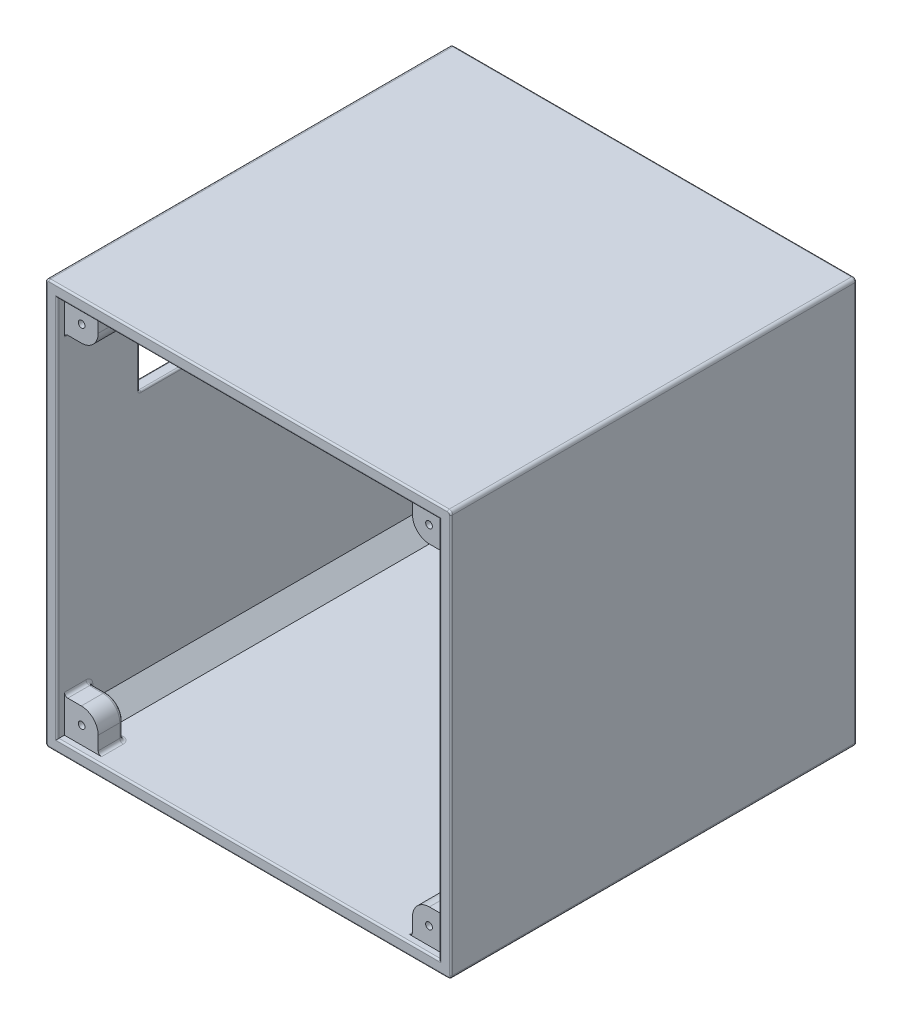
SolidWorks part; units mm, degrees
material "PVC 0.007 Plasticizado"
ref_plane "MESA" through (0, 0, 0) normal (0, 0, 1) x (1, 0, 0)
ref_plane "Plano superior" through (0, 0, 0) normal (0, 1, 0) x (1, 0, 0)
ref_plane "Plano direito" through (0, 0, 0) normal (1, 0, 0) x (0, 0, -1)
sketch "Esboço2" plane through (0, 0, 0) normal (0, 0, 1) x (1, 0, 0)
  line L1 (-60, -60) -> (60, -60)
  line L2 (-60, -60) -> (-60, 60)
  line L3 (-60, 60) -> (60, 60)
  line L4 (60, -60) -> (60, 60)
  line L5 (-60, -60) -> (60, 60) construction
  line L6 (-60, 60) -> (60, -60) construction
  point P0 (0, 0)
extrude "Ressalto-extrusão1" add sketch "Esboço2" along normal blind 120
sketch "Esboço3" plane through (0, 0, 120) normal (0, 0, 1) x (1, 0, 0)
  line L8 (56.5, -56.5) -> (56.5, 56.5)
  line L9 (56.5, 56.5) -> (-56.5, 56.5)
  line L10 (-56.5, 56.5) -> (-56.5, -56.5)
  line L11 (-56.5, -56.5) -> (56.5, -56.5)
  line L12 (56.5, -56.5) -> (56.5, 56.5)
  line L13 (56.5, 56.5) -> (-56.5, 56.5)
  line L14 (-56.5, 56.5) -> (-56.5, -56.5)
  line L15 (-56.5, -56.5) -> (56.5, -56.5)
  dimension "D1" = 3.5
extrude "Corte-extrusão1" cut sketch "Esboço3" against normal blind 120
ref_plane "Plano1" through (0, 0, 0) normal (0, 0, 1) x (1, 0, 0)
ref_plane "Plano2" through (0, 0, 116.5) normal (0, 0, 1) x (1, 0, 0)
sketch "Esboço4" plane through (0, 0, 0) normal (0, 0, 1) x (1, 0, 0)
  line L0 (56.5, 56.5) -> (-56.5, 56.5) construction
  line L1 (-56.5, 56.5) -> (-56.5, -56.5) construction
  line L2 (-51.5, 46.5) -> (-56.5, 46.5)
  line L3 (-56.5, 46.5) -> (-56.5, 56.5)
  line L4 (-56.5, 56.5) -> (-46.5, 56.5)
  line L5 (-46.5, 56.5) -> (-46.5, 51.5)
  line L6 (0, -55) -> (0, 55) construction
  line L7 (46.5, 56.5) -> (46.5, 51.5)
  line L8 (56.5, 56.5) -> (46.5, 56.5)
  line L9 (56.5, 46.5) -> (56.5, 56.5)
  line L10 (51.5, 46.5) -> (56.5, 46.5)
  line L11 (55, 0) -> (-55, 0) construction
  line L12 (51.5, -46.5) -> (56.5, -46.5)
  line L13 (56.5, -46.5) -> (56.5, -56.5)
  line L14 (56.5, -56.5) -> (46.5, -56.5)
  line L15 (46.5, -56.5) -> (46.5, -51.5)
  line L16 (-46.5, -56.5) -> (-46.5, -51.5)
  line L17 (-56.5, -56.5) -> (-46.5, -56.5)
  line L18 (-56.5, -46.5) -> (-56.5, -56.5)
  line L19 (-51.5, -46.5) -> (-56.5, -46.5)
  line L20 (-51.5, 5) -> (-56.5, 5)
  line L21 (-56.5, 5) -> (-56.5, -5)
  line L22 (-56.5, -5) -> (-51.5, -5)
  line L23 (56.5, -5) -> (51.5, -5)
  line L24 (56.5, 5) -> (56.5, -5)
  line L25 (51.5, 5) -> (56.5, 5)
  line L26 (-5, 51.5) -> (-5, 56.5)
  line L27 (-5, 56.5) -> (5, 56.5)
  line L28 (5, 56.5) -> (5, 51.5)
  arc A0 (-51.5, 46.5) -> (-46.5, 51.5) centre (-51.5, 51.5) ccw
  arc A1 (51.5, 46.5) -> (46.5, 51.5) centre (51.5, 51.5) cw
  arc A2 (51.5, -46.5) -> (46.5, -51.5) centre (51.5, -51.5) ccw
  arc A3 (-51.5, -46.5) -> (-46.5, -51.5) centre (-51.5, -51.5) cw
  arc A4 (-51.5, -5) -> (-51.5, 5) centre (-51.5, 0) ccw
  arc A5 (51.5, -5) -> (51.5, 5) centre (51.5, 0) cw
  arc A6 (-5, 51.5) -> (5, 51.5) centre (0, 51.5) ccw
  dimension "D1" = 10
  dimension "D2" = 10
  dimension "D3" = 10
extrude "Ressalto-extrusão2" add sketch "Esboço4" along normal blind 7
sketch "Esboço5" plane through (0, 0, 116.5) normal (0, 0, 1) x (1, 0, 0)
  line L0 (-51.5, 46.5) -> (-56.5, 46.5)
  line L1 (-56.5, 46.5) -> (-56.5, 56.5)
  line L2 (-56.5, 56.5) -> (-46.5, 56.5)
  line L3 (-46.5, 56.5) -> (-46.5, 51.5)
  line L4 (46.5, 56.5) -> (46.5, 51.5)
  line L5 (56.5, 56.5) -> (46.5, 56.5)
  line L6 (56.5, 46.5) -> (56.5, 56.5)
  line L7 (51.5, 46.5) -> (56.5, 46.5)
  line L8 (51.5, -46.5) -> (56.5, -46.5)
  line L9 (56.5, -46.5) -> (56.5, -56.5)
  line L10 (56.5, -56.5) -> (46.5, -56.5)
  line L11 (46.5, -56.5) -> (46.5, -51.5)
  line L12 (-46.5, -56.5) -> (-46.5, -51.5)
  line L13 (-56.5, -56.5) -> (-46.5, -56.5)
  line L14 (-56.5, -46.5) -> (-56.5, -56.5)
  line L15 (-51.5, -46.5) -> (-56.5, -46.5)
  arc A0 (-51.5, 46.5) -> (-46.5, 51.5) centre (-51.5, 51.5) ccw
  arc A1 (51.5, 46.5) -> (46.5, 51.5) centre (51.5, 51.5) cw
  arc A2 (51.5, -46.5) -> (46.5, -51.5) centre (51.5, -51.5) ccw
  arc A3 (-51.5, -46.5) -> (-46.5, -51.5) centre (-51.5, -51.5) cw
  dimension "D1" = 10
ref_plane "Plano5" through (0, 0, 117.9) normal (0, 0, 1) x (1, 0, 0)
sketch "Esboço13" plane through (0, 0, 0) normal (0, 0, 1) x (1, 0, 0)
  line L0 (-56.5, -56.5) -> (56.5, -56.5) construction
  line L1 (-5, -51.5) -> (-5, -56.5)
  line L2 (-5, -56.5) -> (5, -56.5)
  line L3 (5, -56.5) -> (5, -51.5)
  arc A0 (5, -51.5) -> (-5, -51.5) centre (0, -51.5) ccw
  dimension "D1" = 10
extrude "Ressalto-extrusão6" add sketch "Esboço13" along normal blind 7
chamfer "Chanfro1" distance 5 angle 45 1 edges at (-56.5, 56.5, 63.5)
chamfer "Chanfro2" distance 5 angle 45 3 edges at (-56.5, -56.5, 63.5) (56.5, -56.5, 63.5) (56.5, 56.5, 63.5)
sketch "Esboço14" plane through (-60, 0, 0) normal (-1, 0, 0) x (0, 0, 1)
  line L0 (120, 60) -> (0, 60) construction
  line L1 (24.25, 45) -> (95.75, 45)
  line L2 (24.25, 45) -> (24.25, 20.5)
  line L3 (24.25, 20.5) -> (95.75, 20.5)
  line L4 (95.75, 45) -> (95.75, 20.5)
  line L5 (24.25, 45) -> (95.75, 20.5) construction
  line L6 (24.25, 20.5) -> (95.75, 45) construction
  point P0 (60, 32.75)
  point P8 (60, 60)
  dimension "D1" = 71.5
  dimension "D2" = 24.5
  dimension "D3" = 15
extrude "Corte-extrusão6" cut sketch "Esboço14" against normal blind 10
sketch "Esboço15" plane through (0, 0, 120) normal (0, 0, 1) x (1, 0, 0)
  line L1 (-56.5, -56.5) -> (56.5, -56.5)
  line L2 (-56.5, -56.5) -> (-56.5, 56.5)
  line L3 (-56.5, 56.5) -> (56.5, 56.5)
  line L4 (56.5, -56.5) -> (56.5, 56.5)
  line L5 (-56.5, -56.5) -> (56.5, 56.5) construction
  line L6 (-56.5, 56.5) -> (56.5, -56.5) construction
  point P0 (0, 0)
  dimension "D1" = 113
extrude "Corte-extrusão7" cut sketch "Esboço15" against normal blind 5
fillet "Filete3" radius 1 1 edges at (-60, 60, 60)
fillet "Filete4" radius 1 3 edges at (60, 60, 60) (60, -60, 60) (-60, -60, 60)
extrude "Ressalto-extrusão7" add sketch "Esboço5" against normal blind 6 and the other way blind 1.4
fillet "Filete8" radius 1 88 edges at (56.5, 46.5, 3.5) (46.5, 56.5, 3.5) (54, 46.5, 7) (47.9645, 47.9645, 7) (46.5, 54, 7) (49, 56.5, 7) (54, 54, 7) (56.5, 49, 7) (56.5, -46.5, 114.2) (46.5, -56.5, 114.2) (-46.5, -56.5, 114.2) (-56.5, -46.5, 114.2) (-56.5, 46.5, 114.2) (-46.5, 56.5, 114.2) (46.5, 56.5, 114.2) (56.5, 46.5, 114.2) (56.5, 5, 3.5) (56.5, -5, 3.5) (46.5, -56.5, 3.5) (56.5, -46.5, 3.5) (5, -56.5, 3.5) (-5, -56.5, 3.5) (-56.5, -46.5, 3.5) (-46.5, -56.5, 3.5) (-56.5, -5, 3.5) (-56.5, 5, 3.5) (-46.5, 56.5, 3.5) (-56.5, 46.5, 3.5) (-5, 56.5, 3.5) (5, 56.5, 3.5) (54, -46.5, 110.5) (47.9645, -47.9645, 110.5) (46.5, -54, 110.5) (49, -56.5, 110.5) (54, -54, 110.5) (56.5, -49, 110.5) (-49, -56.5, 110.5) (-46.5, -54, 110.5) (-47.9645, -47.9645, 110.5) (-54, -46.5, 110.5) (-56.5, -49, 110.5) (-54, -54, 110.5) (-54, 46.5, 110.5) (-47.9645, 47.9645, 110.5) (-46.5, 54, 110.5) (-49, 56.5, 110.5) (-54, 54, 110.5) (-56.5, 49, 110.5) (49, 56.5, 110.5) (46.5, 54, 110.5) (47.9645, 47.9645, 110.5) (54, 46.5, 110.5) (56.5, 49, 110.5) (54, 54, 110.5) (54, 5, 7) (56.5, 0, 7) (54, -5, 7) (46.5, 0, 7) (46.5, -54, 7) (47.9645, -47.9645, 7) (54, -46.5, 7) (56.5, -49, 7) (54, -54, 7) (49, -56.5, 7) (5, -54, 7) (0, -56.5, 7) (-5, -54, 7) (0, -46.5, 7) (-54, -46.5, 7) (-47.9645, -47.9645, 7) (-46.5, -54, 7) (-49, -56.5, 7) (-54, -54, 7) (-56.5, -49, 7) (-54, -5, 7) (-56.5, 0, 7) (-54, 5, 7) (-46.5, 0, 7) (-46.5, 54, 7) (-47.9645, 47.9645, 7) (-54, 46.5, 7) (-56.5, 49, 7) (-54, 54, 7) (-49, 56.5, 7) (0, 46.5, 7) (-5, 54, 7) (0, 56.5, 7) (5, 54, 7)
sketch "Esboço16" plane through (0, 0, 117.9) normal (0, 0, 1) x (1, 0, 0)
  line L0 (59, 60) -> (-59, 60) construction
  line L1 (-60, 59) -> (-60, -59) construction
  circle A0 centre (-51.4, 51.4) radius 1
  dimension "D1" = 2
  dimension "D2" = 8.6
  dimension "D3" = 8.6
extrude "Corte-extrusão8" cut sketch "Esboço16" against normal up to next (7.4 mm away)
mirror "Espelhar1" about plane through (0, 0, 0) normal (0, 1, 0) of "Corte-extrusão8"
mirror "Espelhar2" about plane through (0, 0, 0) normal (1, 0, 0) of "Espelhar1", "Corte-extrusão8"
sketch "Esboço17" plane through (0, 0, 7) normal (0, 0, 1) x (1, 0, 0)
  line L0 (59, 60) -> (-59, 60) construction
  line L1 (-60, 59) -> (-60, -59) construction
  circle A0 centre (-51.4, 51.4) radius 1.75
  dimension "D1" = 8.6
  dimension "D2" = 8.6
extrude "Corte-extrusão9" cut sketch "Esboço17" against normal up to next (7 mm away)
sketch "Esboço18" plane through (0, 0, 7) normal (0, 0, 1) x (1, 0, 0)
  circle A0 centre (-51.4, 51.4) radius 3.6
  dimension "D1" = 7.2
extrude "Corte-extrusão10" cut sketch "Esboço18" against normal blind 1 and the other way blind 1
mirror "Espelhar5" about plane through (0, 0, 0) normal (0, 1, 0) of "Corte-extrusão10", "Corte-extrusão9"
mirror "Espelhar6" about plane through (0, 0, 0) normal (1, 0, 0) of "Espelhar5", "Corte-extrusão9", "Corte-extrusão10"
sketch "Esboço19" plane through (0, 0, 7) normal (0, 0, 1) x (1, 0, 0)
  line L0 (-60, 59) -> (-60, -59) construction
  line L2 (59, 60) -> (-59, 60) construction
  line L3 (60, -59) -> (60, 59) construction
  line L5 (-59, -60) -> (59, -60) construction
  circle A0 centre (-51.4, 0) radius 3.6
  circle A4 centre (0, 51.4) radius 3.6
  circle A5 centre (51.4, 0) radius 3.6
  circle A6 centre (0, -51.4) radius 3.6
  dimension "D1" = 8.6
  dimension "D3" = 8.6
  dimension "D4" = 7.2
  dimension "D5" = 7.2
  dimension "D6" = 7.2
  dimension "D7" = 7.2
  dimension "8.6" = 8.6
  dimension "D2" = 8.6
extrude "Corte-extrusão12" cut sketch "Esboço19" against normal blind 0.5
sketch "Esboço21" plane through (0, 0, 6.5) normal (0, 0, 1) x (1, 0, 0)
  line L1 (59, 60) -> (-59, 60) construction
  line L2 (60, -59) -> (60, 59) construction
  line L3 (-59, -60) -> (59, -60) construction
  circle A0 centre (-51.4, 0) radius 1.75
  circle A1 centre (0, 51.4) radius 1.75
  circle A2 centre (51.4, 0) radius 1.75
  circle A3 centre (0, -51.4) radius 1.75
  dimension "D1" = 3.5
  dimension "D2" = 8.6
  dimension "D3" = 8.6
  dimension "D4" = 8.6
extrude "Corte-extrusão13" cut sketch "Esboço21" against normal through all
fillet "Filete9" radius 0.5 88 edges at (-59.7071, 59.7071, 120) (-59.7071, 59.7071, 0) (-60, 0, 0) (-60, 0, 120) (-59.7071, -59.7071, 120) (-59.7071, -59.7071, 0) (0, -60, 0) (0, -60, 120) (59.7071, -59.7071, 120) (59.7071, -59.7071, 0) (60, 0, 0) (60, 0, 120) (59.7071, 59.7071, 120) (59.7071, 59.7071, 0) (0, 60, 120) (0, 60, 0) (47.9645, -47.9645, 0) (46.5, -53.5, 0) (46.2071, -56.2071, 0) (25.75, -56.5, 0) (5.2929, -56.2071, 0) (5, -53.5, 0) (0, -46.5, 0) (-5, -53.5, 0) (-5.2929, -56.2071, 0) (-25.75, -56.5, 0) (-46.2071, -56.2071, 0) (-46.5, -53.5, 0) (-47.9645, -47.9645, 0) (-53.5, -46.5, 0) (-56.2071, -46.2071, 0) (-56.5, -25.75, 0) (-56.2071, -5.2929, 0) (-53.5, -5, 0) (-46.5, 0, 0) (-53.5, 5, 0) (-56.2071, 5.2929, 0) (-56.5, 25.75, 0) (-56.2071, 46.2071, 0) (-53.5, 46.5, 0) (-47.9645, 47.9645, 0) (-46.5, 53.5, 0) (-46.2071, 56.2071, 0) (-25.75, 56.5, 0) (-5.2929, 56.2071, 0) (-5, 53.5, 0) (0, 46.5, 0) (5, 53.5, 0) (5.2929, 56.2071, 0) (25.75, 56.5, 0) (46.2071, 56.2071, 0) (46.5, 53.5, 0) (47.9645, 47.9645, 0) (53.5, 46.5, 0) (56.2071, 46.2071, 0) (56.5, 25.75, 0) (56.2071, 5.2929, 0) (53.5, 5, 0) (46.5, 0, 0) (53.5, -5, 0) (56.2071, -5.2929, 0) (56.5, -25.75, 0) (56.2071, -46.2071, 0) (53.5, -46.5, 0) (-53.15, 51.4, 0) (-53.15, -51.4, 0) (49.65, -51.4, 0) (49.65, 51.4, 0) (1.75, -51.4, 0) (53.15, 0, 0) (1.75, 51.4, 0) (-49.65, 0, 0) (-56.5, 20.5, 60) (-60, 20.5, 60) (-56.5, 32.75, 95.75) (-60, 32.75, 95.75) (-58.25, 20.5, 95.75) (-56.5, 45, 60) (-60, 45, 60) (-58.25, 45, 95.75) (-56.5, 32.75, 24.25) (-58.25, 20.5, 24.25) (-60, 32.75, 24.25) (-58.25, 45, 24.25) (0, 56.5, 120) (-56.5, 0, 120) (0, -56.5, 120) (56.5, 0, 120)
